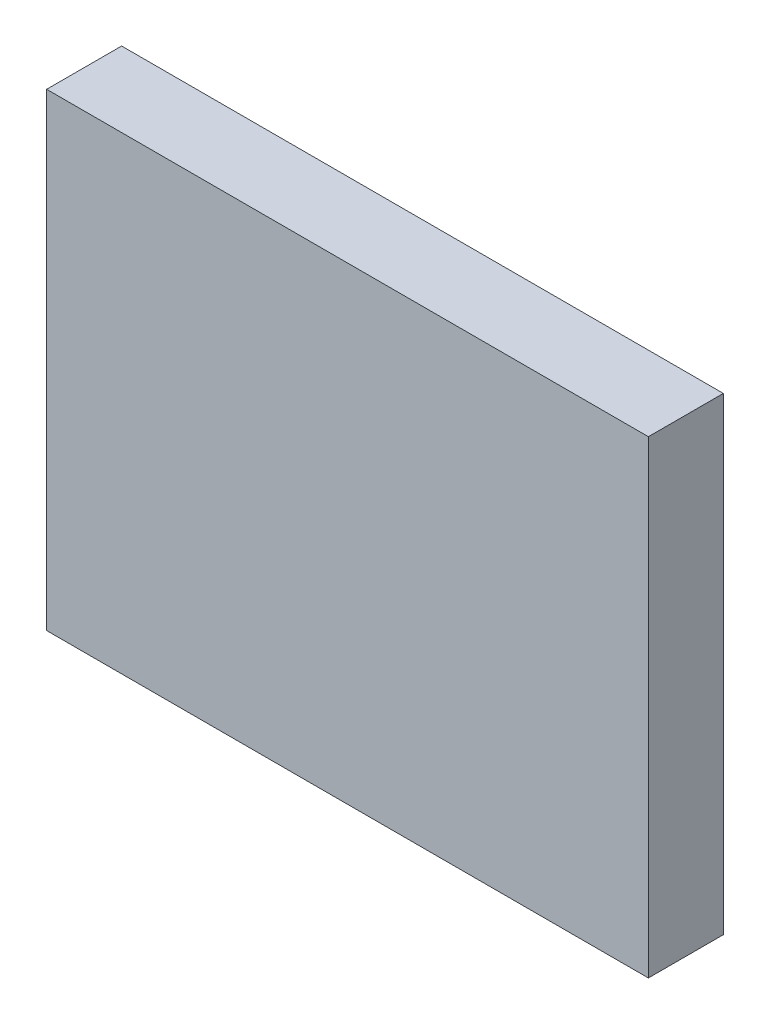
SolidWorks part; units mm, degrees
ref_plane "Front Plane" through (0, 0, 0) normal (0, 0, 1) x (1, 0, 0)
ref_plane "Top Plane" through (0, 0, 0) normal (0, 1, 0) x (1, 0, 0)
ref_plane "Right Plane" through (0, 0, 0) normal (1, 0, 0) x (0, 0, -1)
sketch "Sketch1" plane through (0, 0, 0) normal (0, 0, 1) x (1, 0, 0)
  line L0 (-4.0135, 2.4435) -> (4.0135, 2.4435)
  line L1 (4.0135, 2.4435) -> (4.0135, -3.81)
  line L2 (4.0135, -3.81) -> (-4.0135, -3.81)
  line L3 (-4.0135, -3.81) -> (-4.0135, 2.4435)
extrude "Component_Outline" add sketch "Sketch1" along normal blind 1 separate body
sketch3d "3DSketch1"
  line L0 (0, 0, 0) -> (1, 0, 0)
  line L1 (0, 0, 0) -> (0, 1, 0)
  line L2 (0, 0, 0) -> (0, 0, 1)
  point P0 (0, 0, 0)
